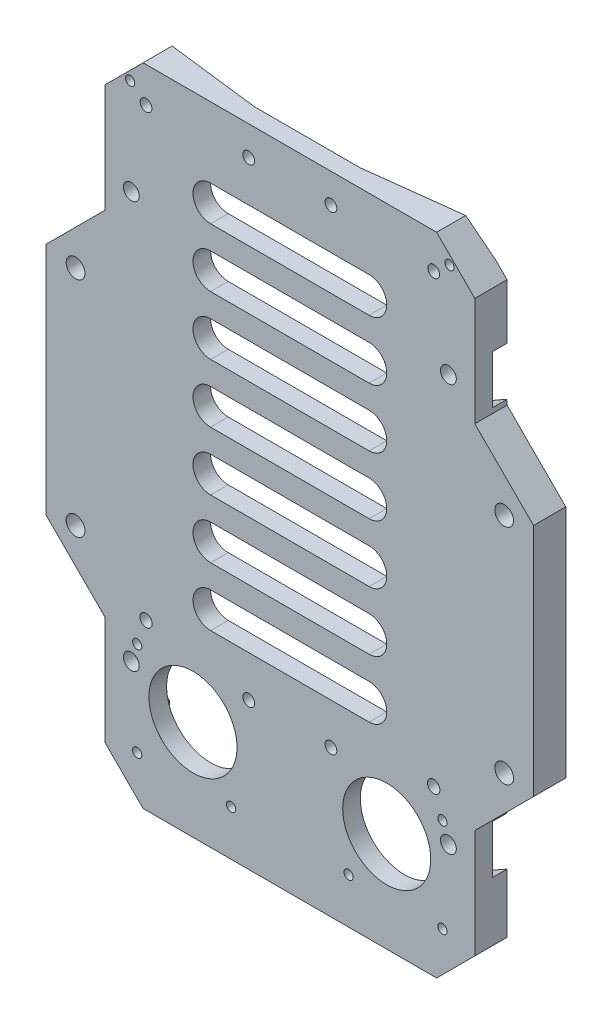
SolidWorks part; units mm, degrees
ref_plane "前视基准面" through (0, 0, 0) normal (0, 0, 1) x (1, 0, 0)
ref_plane "上视基准面" through (0, 0, 0) normal (0, 1, 0) x (1, 0, 0)
ref_plane "右视基准面" through (0, 0, 0) normal (1, 0, 0) x (0, 0, -1)
sketch "草图1" plane through (0, 0, 0) normal (0, 1, 0) x (1, 0, 0)
  line L0 (-46.859, -0.3436) -> (-46.859, 2.6564)
  line L1 (-24.359, -0.0836) -> (-6.359, -0.0836)
  line L2 (-24.359, -3.0836) -> (-46.859, -3.0836)
  line L3 (16.141, -0.3436) -> (16.141, 2.6603)
  line L4 (-46.859, 2.6564) -> (-24.359, -0.0836)
  line L5 (-6.359, -3.0836) -> (-24.359, -3.0836)
  line L9 (-6.359, -0.0836) -> (16.141, 2.6603)
  line L10 (-46.859, -3.0836) -> (-46.859, -0.3436)
  line L11 (-6.359, -3.0836) -> (16.141, -3.0836)
  line L12 (16.141, -3.0836) -> (16.141, -0.3436)
  line L14 (16.141, 8.2714) -> (16.141, 2.6603) construction
  line L15 (15.416, 2.5719) -> (16.141, 2.6603) construction
  dimension "D1" = 3
  dimension "D2" = 22.5
  dimension "D3" = 18
  dimension "D4" = 22.5
  dimension "D5" = 2.74
  dimension "D6" = 2.74
  dimension "D7" = 3
  dimension "D8" = 3
extrude "凸台-拉伸1" add sketch "草图1" along normal blind 110
sketch "草图3" plane through (0, 0, 3.0836) normal (0, 0, 1) x (1, 0, 0)
  line L0 (16.141, 110) -> (16.141, 0) construction
  line L1 (-46.859, 110) -> (16.141, 110) construction
  line L2 (-15.359, 110) -> (-15.359, 0) construction
  line L3 (-46.859, 0) -> (16.141, 0) construction
  circle A0 centre (11.641, 90) radius 1.35
  circle A1 centre (11.641, 20.7) radius 1.35
  circle A2 centre (-42.359, 20.7) radius 1.35
  circle A3 centre (-42.359, 90) radius 1.35
  dimension "D1" = 4.5
  dimension "D2" = 20
  dimension "D3" = 69.3
extrude "切除-拉伸2" cut sketch "草图3" against normal blind 110
sketch "草图4" plane through (0, 0, 0.0836) normal (0, 0, -1) x (-1, 0, 0)
  line L0 (42.359, 20.7) -> (42.359, 90) construction
  line L1 (40.909, 6.9) -> (40.909, 13.2)
  line L2 (42.359, 20.7) -> (31.3616, 20.7) construction
  line L3 (42.359, 90) -> (31.3616, 90) construction
  line L4 (15.359, 0) -> (15.359, 110) construction
  line L5 (6.359, 0) -> (24.359, 0) construction
  line L6 (6.359, 110) -> (24.359, 110) construction
  line L7 (40.909, 6.9) -> (-10.191, 6.9)
  line L8 (40.909, 103.8) -> (-10.191, 103.8)
  line L9 (-10.191, 6.9) -> (-10.191, 13.2)
  line L10 (40.909, 13.2) -> (47.0939, 16.7)
  line L11 (40.909, 28.2) -> (47.0939, 24.7)
  line L12 (47.0939, 16.7) -> (47.0939, 24.7)
  line L13 (40.909, 28.2) -> (40.909, 82.5)
  line L14 (-10.191, 55.35) -> (29.572, 55.35) construction
  line L15 (40.909, 82.5) -> (47.0939, 86)
  line L16 (47.0939, 94) -> (47.0939, 86)
  line L17 (40.909, 97.5) -> (47.0939, 94)
  line L18 (40.909, 97.5) -> (40.909, 103.8)
  line L19 (-10.191, 97.5) -> (-16.3759, 94)
  line L20 (-16.3759, 94) -> (-16.3759, 86)
  line L21 (-10.191, 82.5) -> (-16.3759, 86)
  line L22 (-10.191, 28.2) -> (-16.3759, 24.7)
  line L23 (-16.3759, 16.7) -> (-16.3759, 24.7)
  line L24 (-10.191, 13.2) -> (-16.3759, 16.7)
  line L25 (-10.191, 28.2) -> (-10.191, 82.5)
  line L26 (-10.191, 97.5) -> (-10.191, 103.8)
  point P17 (15.359, 103.8)
  point P18 (15.359, 6.9)
  dimension "D1" = 2.9
  dimension "D2" = 13.8
  dimension "D3" = 13.8
  dimension "D4" = 7.5
  dimension "D5" = 4
extrude "切除-拉伸3" cut sketch "草图4" along normal blind 65
sketch "Sketch1" plane through (0, 0, 3.0836) normal (0, 0, 1) x (1, 0, 0)
  line L0 (-15.359, 110) -> (-15.359, 0) construction
  line L1 (-46.859, 110) -> (16.141, 110) construction
  line L2 (-46.859, 0) -> (16.141, 0) construction
  circle A0 centre (-42.5589, 106.2656) radius 0.785
  circle A1 centre (-39.8589, 104) radius 1
  circle A2 centre (-22.3588, 105) radius 1
  circle A3 centre (-22.3588, 25) radius 1
  arc A4 (-22.3588, 24) -> (-22.3588, 26) centre (-22.3588, 25) ccw construction
  circle A5 centre (-39.8589, 28) radius 1.05
  circle A6 centre (-41.359, 23.75) radius 0.785
  circle A7 centre (-41.359, 7.75) radius 0.785
  arc A8 (-41.359, 8.535) -> (-42.144, 7.75) centre (-41.359, 7.75) ccw construction
  circle A9 centre (-25.359, 7.75) radius 0.785
  circle A10 centre (-5.359, 7.75) radius 0.785
  circle A11 centre (10.641, 7.75) radius 0.785
  circle A12 centre (10.641, 23.75) radius 0.785
  circle A13 centre (9.1409, 28) radius 1.05
  circle A14 centre (-8.3592, 25) radius 1
  circle A15 centre (-8.3592, 105) radius 1
  circle A16 centre (9.1409, 104) radius 1
  circle A17 centre (11.8409, 106.2656) radius 0.785
extrude "Cut-Extrude1" cut sketch "Sketch1" against normal blind 10
ref_plane "Plane1" through (0, 0, -2.4164) normal (0, 0, -1) x (-1, 0, 0)
sketch "Sketch2" plane through (0, 0, -2.4164) normal (0, 0, -1) x (-1, 0, 0)
  line L1 (-19.1434, 137.9044) -> (51.8259, 137.9044)
  line L2 (-19.1434, 137.9044) -> (-19.1434, -21.7945)
  line L3 (-19.1434, -21.7945) -> (51.8259, -21.7945)
  line L4 (51.8259, 137.9044) -> (51.8259, -21.7945)
extrude "Cut-Extrude2" cut sketch "Sketch2" along normal blind 10
sketch "Sketch3" plane through (0, 0, 3.0836) normal (0, 0, 1) x (1, 0, 0)
  line L0 (-46.859, 55) -> (36.4072, 55) construction
  line L1 (-46.859, 110) -> (-46.859, 0) construction
  line L2 (-15.359, 110) -> (-15.359, 0) construction
  line L3 (-46.859, 110) -> (16.141, 110) construction
  line L4 (-46.859, 0) -> (16.141, 0) construction
  line L5 (-46.859, 85) -> (-56.859, 75)
  line L6 (-56.859, 75) -> (-56.859, 35)
  line L7 (-56.859, 35) -> (-46.859, 25)
  line L8 (-46.859, 85) -> (-46.859, 25)
  line L9 (16.141, 85) -> (16.141, 25)
  line L10 (26.141, 35) -> (16.141, 25)
  line L11 (26.141, 75) -> (26.141, 35)
  line L12 (16.141, 85) -> (26.141, 75)
  dimension "D1" = 30
  dimension "D2" = 30
  dimension "D3" = 45
  dimension "D4" = 45
  dimension "D5" = 10
extrude "Boss-Extrude1" add sketch "Sketch3" against normal up to vertex (5.5 mm away)
sketch "Sketch4" plane through (0, 0, -2.4164) normal (0, 0, -1) x (-1, 0, 0)
  circle A0 centre (-21.141, 74) radius 1.6
  circle A1 centre (-21.141, 36) radius 1.6
  circle A2 centre (51.859, 74) radius 1.6
  circle A3 centre (51.859, 36) radius 1.6
extrude "Cut-Extrude3" cut sketch "Sketch4" against normal blind 20
chamfer "Chamfer1" distance 6.5 angle 45 4 edges at (16.141, 110, 0.3336) (-46.859, 110, 0.3336) (16.141, 0, 0.3336) (-46.859, 0, 0.3336)
sketch "Sketch5" plane through (0, 0, 0.0836) normal (0, 0, -1) x (-1, 0, 0)
  line L0 (24.359, 0) -> (40.359, 0) construction
  line L1 (-9.641, 0) -> (6.359, 0) construction
  line L2 (46.859, 24.8329) -> (46.859, 16.5671) construction
  line L3 (-16.141, 16.5671) -> (-16.141, 24.8329) construction
  line L4 (28.859, 35) -> (1.859, 35) construction
  line L5 (28.859, 32) -> (1.859, 32)
  line L6 (28.859, 38) -> (1.859, 38)
  line L7 (6.359, 0) -> (24.359, 0) construction
  line L8 (28.859, 45) -> (1.859, 45) construction
  line L9 (28.859, 42) -> (1.859, 42)
  line L10 (28.859, 48) -> (1.859, 48)
  line L11 (28.859, 55) -> (1.859, 55) construction
  line L12 (28.859, 52) -> (1.859, 52)
  line L13 (28.859, 58) -> (1.859, 58)
  line L14 (28.859, 65) -> (1.859, 65) construction
  line L15 (28.859, 62) -> (1.859, 62)
  line L16 (28.859, 68) -> (1.859, 68)
  line L17 (28.859, 75) -> (1.859, 75) construction
  line L18 (28.859, 72) -> (1.859, 72)
  line L19 (28.859, 78) -> (1.859, 78)
  line L20 (28.859, 85) -> (1.859, 85) construction
  line L21 (28.859, 82) -> (1.859, 82)
  line L22 (28.859, 88) -> (1.859, 88)
  line L23 (28.859, 95) -> (1.859, 95) construction
  line L24 (28.859, 92) -> (1.859, 92)
  line L25 (28.859, 98) -> (1.859, 98)
  circle A0 centre (31.859, 17) radius 7.5
  circle A1 centre (-1.141, 17) radius 7.5
  arc A2 (28.859, 32) -> (28.859, 38) centre (28.859, 35) ccw
  arc A3 (1.859, 38) -> (1.859, 32) centre (1.859, 35) ccw
  arc A4 (28.859, 42) -> (28.859, 48) centre (28.859, 45) ccw
  arc A5 (1.859, 48) -> (1.859, 42) centre (1.859, 45) ccw
  arc A6 (28.859, 52) -> (28.859, 58) centre (28.859, 55) ccw
  arc A7 (1.859, 58) -> (1.859, 52) centre (1.859, 55) ccw
  arc A8 (28.859, 62) -> (28.859, 68) centre (28.859, 65) ccw
  arc A9 (1.859, 68) -> (1.859, 62) centre (1.859, 65) ccw
  arc A10 (28.859, 72) -> (28.859, 78) centre (28.859, 75) ccw
  arc A11 (1.859, 78) -> (1.859, 72) centre (1.859, 75) ccw
  arc A12 (28.859, 82) -> (28.859, 88) centre (28.859, 85) ccw
  arc A13 (1.859, 88) -> (1.859, 82) centre (1.859, 85) ccw
  arc A14 (28.859, 92) -> (28.859, 98) centre (28.859, 95) ccw
  arc A15 (1.859, 98) -> (1.859, 92) centre (1.859, 95) ccw
  point P14 (15.359, 35)
  point P24 (15.359, 45)
  point P31 (15.359, 55)
  point P38 (15.359, 65)
  point P45 (15.359, 75)
  point P52 (15.359, 85)
  point P59 (15.359, 95)
  dimension "D1" = 17
  dimension "D2" = 17
  dimension "D3" = 15
  dimension "D4" = 15
  dimension "D5" = 15
  dimension "D6" = 3
  dimension "D7" = 18
  dimension "D8" = 18
  dimension "D9" = 35
  dimension "D10" = 7
extrude "Cut-Extrude4" cut sketch "Sketch5" against normal blind 10
